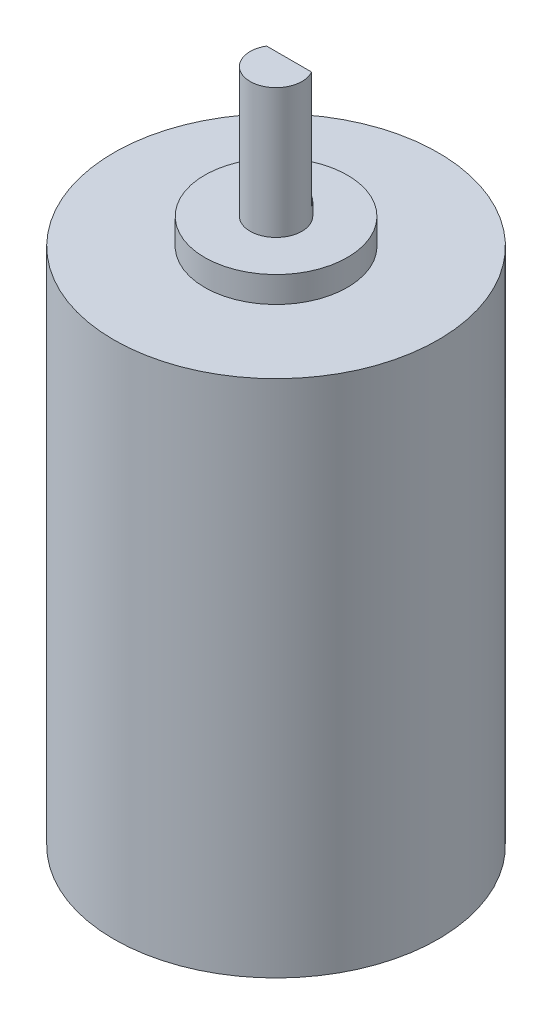
SolidWorks part; units mm, degrees
ref_plane "Plano frontal" through (0, 0, 0) normal (0, 0, 1) x (1, 0, 0)
ref_plane "Plano superior" through (0, 0, 0) normal (0, 1, 0) x (1, 0, 0)
ref_plane "Plano direito" through (0, 0, 0) normal (1, 0, 0) x (0, 0, -1)
sketch "Esboço1" plane through (0, 0, 0) normal (0, 0, 1) x (1, 0, 0)
  line L0 (0, 0) -> (12.5, 0)
  line L1 (12.5, 0) -> (12.5, 40)
  line L2 (12.5, 40) -> (5.5, 40)
  line L3 (5.5, 40) -> (5.5, 42)
  line L4 (5.5, 42) -> (2, 42)
  line L5 (2, 42) -> (2, 52)
  line L6 (0, 52) -> (0, 0) construction
  line L7 (0, 0) -> (0, 52)
  line L8 (0, 52) -> (2, 52)
  dimension "D1" = 52
  dimension "D2" = 10
  dimension "D3" = 2
  dimension "D4" = 4
  dimension "D5" = 11
  dimension "D6" = 25
revolve "Revolução1" add sketch "Esboço1" angle 360 about L6
sketch "Esboço2" plane through (0, 52, 0) normal (0, 1, 0) x (1, 0, 0)
  line L0 (-2, 0) -> (2, 0) construction
  line L1 (-1.7321, 1) -> (1.7321, 1)
  line L2 (0, 1) -> (0, -2) construction
  arc A0 (-1.7321, 1) -> (1.7321, 1) centre (0, 0) ccw
  dimension "D1" = 3
extrude "Corte-Extrusão-Fina1" cut sketch "Esboço2" against normal blind 9 thin thin type one direction wall 10
